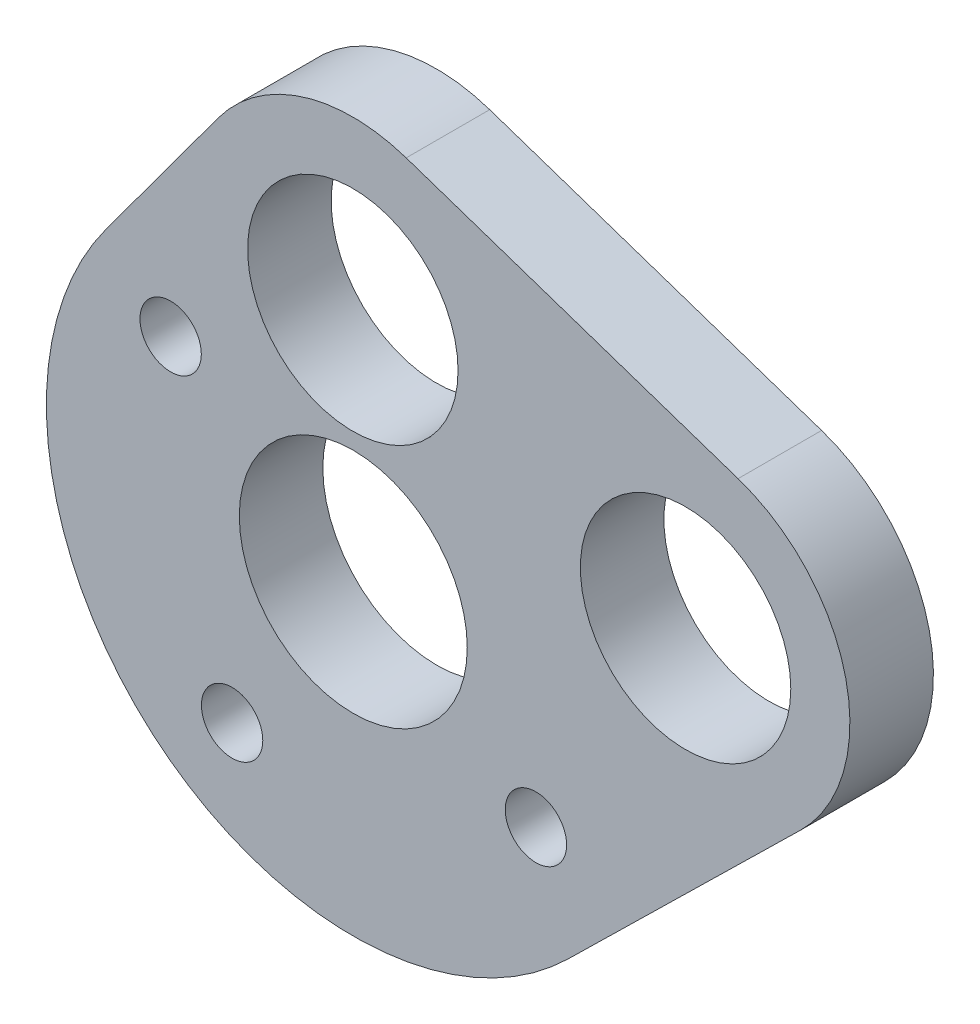
SolidWorks part; units mm, degrees
ref_plane "Front Plane" through (0, 0, 0) normal (0, 0, 1) x (1, 0, 0)
ref_plane "Top Plane" through (0, 0, 0) normal (0, 1, 0) x (1, 0, 0)
ref_plane "Right Plane" through (0, 0, 0) normal (1, 0, 0) x (0, 0, -1)
sketch "Sketch1" plane through (0, 0, 0) normal (0, 0, 1) x (1, 0, 0)
  line L0 (0, -0.5945) -> (-0.0251, 12.827) construction
  line L1 (-0.0251, 12.827) -> (18.9495, 6.5927) construction
  line L2 (18.9495, 6.5927) -> (0, -0.5945) construction
  line L3 (0, -0.5945) -> (-10.4159, 6.3162) construction
  line L4 (0, -0.5945) -> (-10.4159, 6.3162) construction
  line L5 (0, -0.5945) -> (-6.9107, -11.0105) construction
  line L6 (3.0173, 21.853) -> (21.943, 15.4737)
  line L7 (25.5084, -0.1015) -> (12.2474, -13.0946)
  line L8 (-14.0951, 9.7775) -> (-7.6969, 18.4723)
  circle A0 centre (-0.0251, 12.827) radius 6
  circle A1 centre (18.9495, 6.5927) radius 6
  circle A2 centre (0, -0.5945) radius 6.5
  circle A3 centre (0, -0.5945) radius 12.5 construction
  circle A4 centre (-10.4159, 6.3162) radius 1.75
  circle A5 centre (-6.9107, -11.0105) radius 1.75
  circle A6 centre (10.4159, -7.5053) radius 1.75
  arc A7 (-14.0951, 9.7775) -> (12.2474, -13.0946) centre (0, -0.5945) ccw
  arc A9 (25.5084, -0.1015) -> (21.943, 15.4737) centre (18.9495, 6.5927) ccw
  arc A11 (3.0173, 21.853) -> (-7.6969, 18.4723) centre (-0.0251, 12.827) ccw
  dimension "D1" = 13
  dimension "D2" = 25
  dimension "D3" = 3.5
  dimension "D6" = 35
  dimension "D7" = 19.9725
  dimension "D5" = 90
  dimension "D4" = 3
extrude "Boss-Extrude1" add sketch "Sketch1" along normal blind 4.7625
